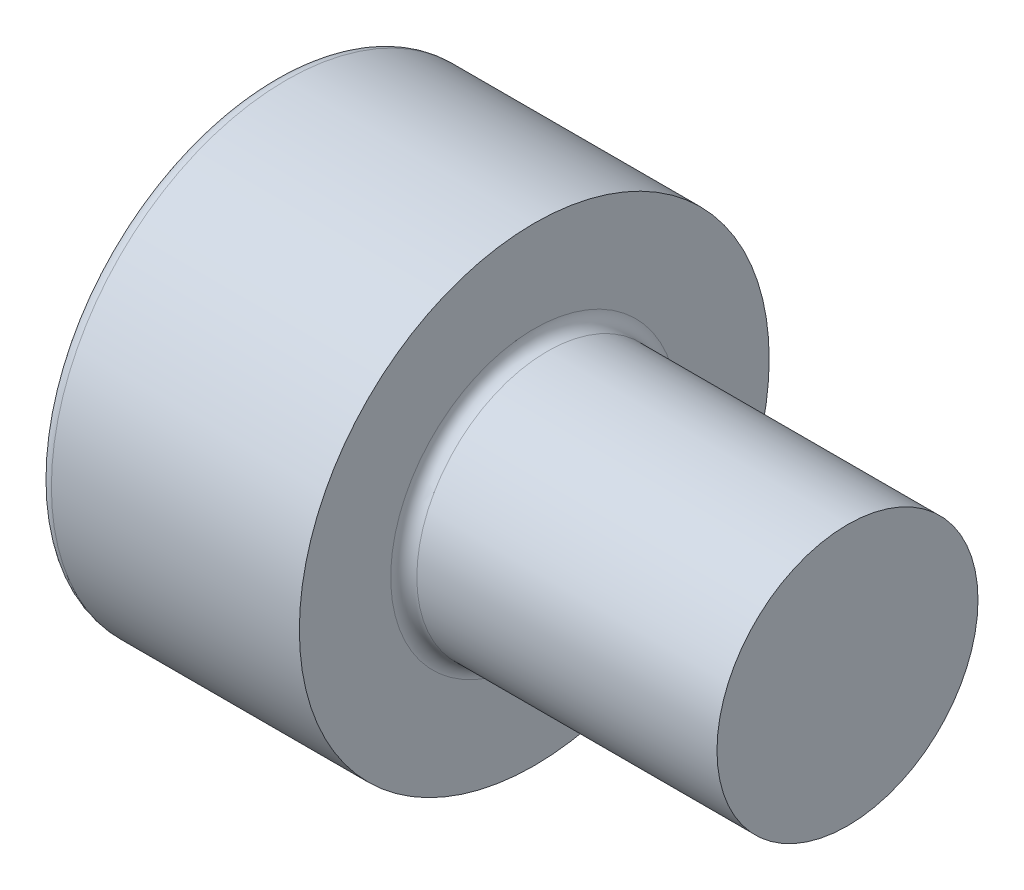
SolidWorks part; units mm, degrees
material "1023 Carbon Steel Sheet (SS)"
ref_plane "Front Plane" through (0, 0, 0) normal (0, 0, 1) x (1, 0, 0)
ref_plane "Top Plane" through (0, 0, 0) normal (0, 1, 0) x (1, 0, 0)
ref_plane "Right Plane" through (0, 0, 0) normal (1, 0, 0) x (0, 0, -1)
ref_plane "Plane1" through (0, 0, 0) normal (0, 0, -1) x (-1, 0, 0)
sketch "Sketch1" plane through (0, 0, 0) normal (0, 0, -1) x (-1, 0, 0)
  line L0 (-2.5, 2.25) -> (-2.5, 0)
  line L1 (-2.5, 0) -> (0, 0)
  line L2 (0, 0) -> (0, 2.25)
  line L3 (0, 2.25) -> (-2.5, 2.25)
  line L4 (-2.5, 0) -> (0, 0) construction
revolve "Revolve1" add sketch "Sketch1" angle 360 about L4
sketch "Sketch2" plane through (2.5, 0, 0) normal (1, 0, 0) x (0, 0, -1)
  circle A0 centre (0, 0) radius 1.25
extrude "Boss-Extrude1" add sketch "Sketch2" along normal blind 8
sketch "Sketch3" plane through (0, 0, 0) normal (-1, 0, 0) x (0, 0, 1)
  line L0 (-1.0225, -0.5903) -> (0, -1.1807)
  line L1 (0, -1.1807) -> (1.0225, -0.5903)
  line L2 (1.0225, -0.5903) -> (1.0225, 0.5903)
  line L3 (1.0225, 0.5903) -> (0, 1.1807)
  line L4 (0, 1.1807) -> (-1.0225, 0.5903)
  line L5 (-1.0225, 0.5903) -> (-1.0225, -0.5903)
extrude "Cut-Extrude1" cut sketch "Sketch3" against normal blind 1.1
sketch "Sketch4" plane through (0, 0, 0) normal (0, 0, 1) x (1, 0, 0)
  line L0 (1.1, 1.0225) -> (1.1, 0)
  line L1 (1.1, 0) -> (1.6903, 0)
  line L2 (1.6903, 0) -> (1.1, 1.0225)
  line L3 (1.1, 0) -> (1.6904, 0) construction
revolve "Cut-Revolve1" cut sketch "Sketch4" angle 360 about L3
chamfer "Chamfer1" distance 0.2535 angle 45 1 edges at (10.5, 0, -1.25)
fillet "Fillet1" radius 0.125 2 edges at (2.5, 0, -1.25) (0, 0, 2.25)
sketch "Sketch5" plane through (0, 0, 0) normal (0, 0, 1) x (1, 0, 0)
  line L0 (10.5, -0.9965) -> (10.5, 0.9965) construction
  line L1 (10.5, -2.709) -> (5.5, -2.709)
  line L2 (10.5, -2.709) -> (10.5, 1.9008)
  line L3 (10.5, 1.9008) -> (5.5, 1.9008)
  line L4 (5.5, -2.709) -> (5.5, 1.9008)
  dimension "D1" = 5
extrude "Cut-Extrude2" cut sketch "Sketch5" against normal blind 10 and the other way blind 10
